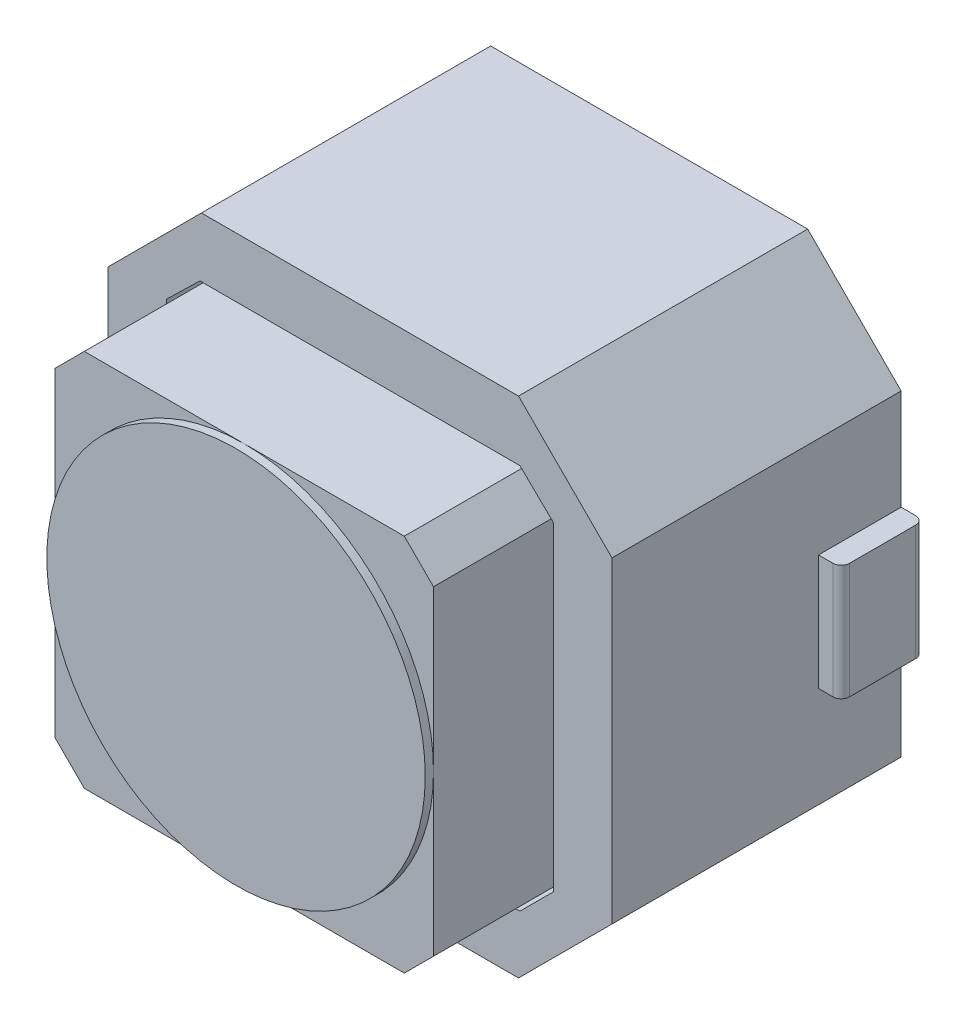
SolidWorks part; units mm, degrees
ref_plane "Front" through (0, 0, 0) normal (0, 0, 1) x (1, 0, 0)
ref_plane "Top" through (0, 0, 0) normal (0, 1, 0) x (1, 0, 0)
ref_plane "Right" through (0, 0, 0) normal (1, 0, 0) x (0, 0, -1)
sketch "草图1" plane through (0, 0, 0) normal (0, 0, 1) x (1, 0, 0)
  line L0 (0, 0) -> (0, 0.8795) construction
  line L1 (-1.9186, -3.05) -> (1.9186, -3.05)
  line L2 (-3.05, -1.9186) -> (-3.05, 1.9186)
  line L3 (-1.9186, 3.05) -> (1.9186, 3.05)
  line L4 (3.05, -1.9186) -> (3.05, 1.9186)
  line L5 (-3.05, -3.05) -> (3.05, 3.05) construction
  line L6 (-2.4843, 2.4843) -> (3.05, -3.05) construction
  line L7 (0, 0) -> (1.5916, 0) construction
  line L8 (-1.9186, 3.05) -> (-3.05, 1.9186)
  line L9 (3.05, -1.9186) -> (1.9186, -3.05)
  line L10 (1.9186, 3.05) -> (3.05, 1.9186)
  line L11 (-3.05, -1.9186) -> (-1.9186, -3.05)
  point P0 (0, 0)
extrude "凸台-拉伸1" add sketch "草图1" along normal blind 3.5
sketch "草图2" plane through (0, 0, 3.5) normal (0, 0, 1) x (1, 0, 0)
  line L0 (2.29, -1.9364) -> (1.9364, -2.29)
  line L1 (1.9364, -2.29) -> (-1.9364, -2.29)
  line L2 (2.29, -1.9364) -> (2.29, 1.9364)
  line L3 (1.9364, 2.29) -> (-1.9364, 2.29)
  line L4 (-2.29, -1.9364) -> (-2.29, 1.9364)
  line L5 (2.29, -2.29) -> (-2.29, 2.29) construction
  line L6 (2.29, 2.29) -> (-2.29, -2.29) construction
  line L7 (0, 0) -> (0, 0.4886) construction
  line L8 (-1.9364, 2.29) -> (-2.29, 1.9364)
  line L9 (0, 0) -> (0.6891, 0) construction
  line L10 (-1.9364, -2.29) -> (-2.29, -1.9364)
  line L11 (1.9364, 2.29) -> (2.29, 1.9364)
  circle A0 centre (0, 0) radius 2.29 construction
extrude "凸台-拉伸2" add sketch "草图2" along normal blind 1.5
sketch "草图3" plane through (0, 0, 5) normal (0, 0, 1) x (1, 0, 0)
  circle A0 centre (0, 0) radius 2.29
extrude "切除-拉伸1" cut sketch "草图3" against normal blind 0.1 flip side to cut
sketch "草图4" plane through (-3.05, 0, 0) normal (-1, 0, 0) x (0, 0, 1)
  line L0 (0, -0.7) -> (0, 0.7)
  line L1 (0, -0.7) -> (1, -0.7)
  line L3 (0, 0.7) -> (1, 0.7)
  line L4 (1, -0.7) -> (1, 0.7)
  line L5 (-1, -0.7) -> (1, 0.7) construction
  line L6 (-1, 0.7) -> (1, -0.7) construction
  point P0 (0, 0)
extrude "凸台-拉伸3" add sketch "草图4" along normal blind 0.275
fillet "圆角1" radius 0.1 2 edges at (-3.325, 0, 0) (-3.325, 0, 1)
mirror "镜向1" about plane through (0, 0, 0) normal (1, 0, 0) of "切除-拉伸1", "圆角1", "凸台-拉伸3"
sketch "草图5" plane through (0, 0, 3.5) normal (0, 0, 1) x (1, 0, 0)
  line L0 (-2.29, 1.9364) -> (-1.9364, 2.29)
  line L1 (-1.9364, 2.29) -> (1.9364, 2.29)
  line L2 (2.29, 1.9364) -> (1.9364, 2.29) construction
  line L3 (2.29, 1.9364) -> (1.9364, 2.29) construction
  line L4 (1.9364, 2.29) -> (2.29, 1.9364)
  line L5 (2.29, 1.9364) -> (2.29, -1.9364)
  line L6 (2.29, -1.9364) -> (1.9364, -2.29)
  line L7 (1.9364, -2.29) -> (-1.9364, -2.29)
  line L8 (-1.9364, -2.29) -> (-2.29, -1.9364)
  line L9 (-2.29, -1.9364) -> (-1.9364, -2.29) construction
  line L10 (-2.29, -1.9364) -> (-1.9364, -2.29) construction
  line L11 (-2.29, -1.9364) -> (-2.29, 1.9364)
  line L12 (-2.29, 1.9364) -> (-2.34, 1.9364) construction
  line L13 (-2.34, 1.9364) -> (-2.34, -1.9364)
  line L14 (-2.34, -1.9364) -> (-1.9364, -2.34)
  line L15 (-1.9364, -2.34) -> (1.9364, -2.34)
  line L16 (1.9364, -2.34) -> (2.34, -1.9364)
  line L17 (2.34, -1.9364) -> (2.34, 1.9364)
  line L18 (2.34, 1.9364) -> (1.9364, 2.3289)
  line L19 (1.9364, 2.3289) -> (-1.9364, 2.3289)
  line L20 (-1.9364, 2.3289) -> (-2.34, 1.9364)
extrude "切除-拉伸2" cut sketch "草图5" against normal blind 2
